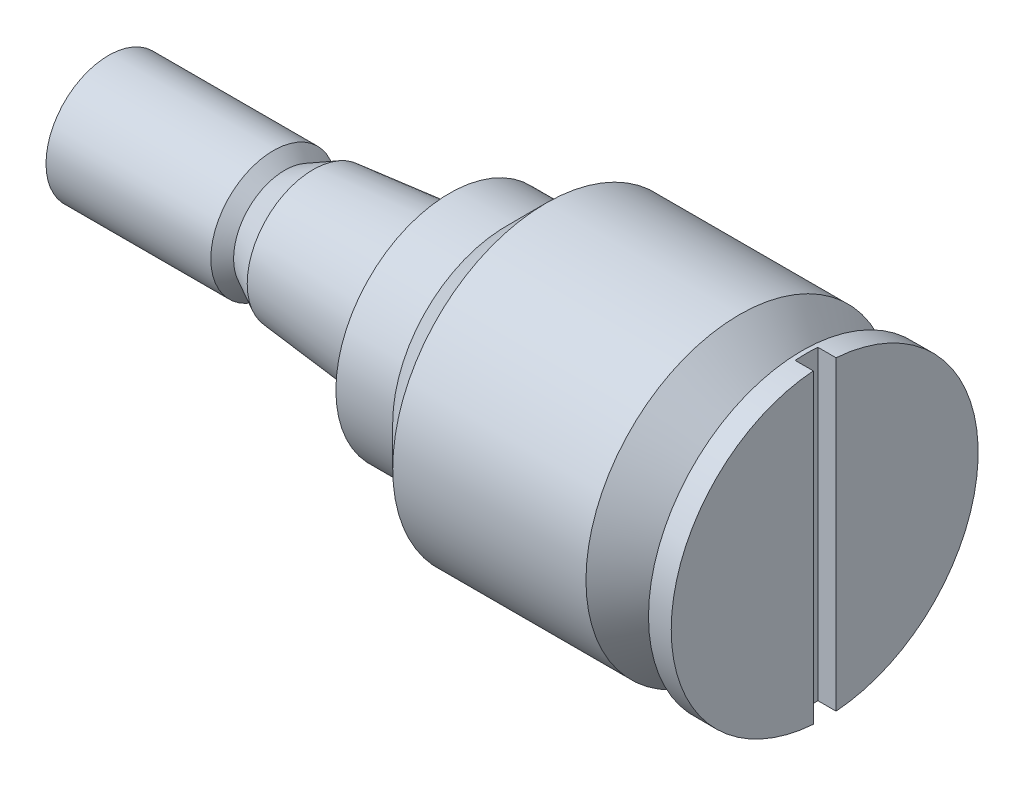
SolidWorks part; units mm, degrees
ref_plane "Спереди" through (0, 0, 0) normal (0, 0, 1) x (1, 0, 0)
ref_plane "Сверху" through (0, 0, 0) normal (0, 1, 0) x (1, 0, 0)
ref_plane "Справа" through (0, 0, 0) normal (1, 0, 0) x (0, 0, -1)
sketch "Эскиз1" plane through (0, 0, 0) normal (0, 0, 1) x (1, 0, 0)
  line L0 (-31.5, 0) -> (31.5, 0)
  line L1 (31.5, 0) -> (31.5, 13.5)
  line L2 (31.5, 13.5) -> (29.5, 13.5)
  line L3 (29.5, 13.5) -> (29.5, 10)
  line L4 (29.5, 10) -> (27.5, 10)
  line L5 (27.5, 10) -> (24, 13.5)
  line L6 (24, 13.5) -> (7, 13.5)
  line L7 (7, 13.5) -> (3.5, 10)
  line L8 (-1.5, 7) -> (-1.5, 10)
  line L9 (-1.5, 7) -> (-13.5, 5.8)
  line L10 (-1.5, 10) -> (3.5, 10)
  line L11 (-31.5, 5.5) -> (-31.5, 0)
  line L12 (-320.1149, 10.8197) -> (-320.1149, 0.8197) construction
  line L13 (-320.1149, 0.8197) -> (-420.1149, 0.8197) construction
  line L14 (-420.1149, 0.8197) -> (-320.1149, 10.8197) construction
  line L15 (-31.5, 5.5) -> (-17, 5.5)
  line L16 (-17, 5.5) -> (-16, 4.5)
  line L17 (-16, 4.5) -> (-13.5, 5.8)
  line L18 (-261.9182, 0) -> (229.0654, 0) construction
  point P21 (0, 0)
  dimension "D1" = 100
  dimension "D2" = 10
  dimension "D3" = 1
  dimension "d_1" = 11
  dimension "l_2" = 2.5
  dimension "l_ps" = 45
  dimension "d_r" = 20
  dimension "d_p" = 14
  dimension "l_1" = 2
  dimension "l_v" = 28
  dimension "d_2" = 20
  dimension "l_p" = 63
  dimension "s_" = 5
  dimension "D4" = 1
  dimension "d_g" = 27
  dimension "D5" = 2
  dimension "d_v" = 27
  dimension "D6" = 45
revolve "Повернуть1" add sketch "Эскиз1" angle 360 about L18
sketch "Эскиз2" plane through (0, 0, 0) normal (0, 1, 0) x (1, 0, 0)
  line L0 (31.5, -13.5) -> (31.5, 13.5) construction
  line L1 (31.5, 1) -> (29.9, 1)
  line L2 (31.5, 1) -> (31.5, -1)
  line L3 (31.5, -1) -> (29.9, -1)
  line L4 (29.9, 1) -> (29.9, -1)
  line L5 (31.5, 1) -> (29.9, -1) construction
  line L6 (31.5, -1) -> (29.9, 1) construction
  point P0 (30.7, 0)
  dimension "D1" = 2
  dimension "D2" = 1.6
extrude "Вырез-Вытянуть1" cut sketch "Эскиз2" against normal through all both and the other way through all
equation "\"d_1\" = 11"
equation "\"d_1@Эскиз1\"=\"d_1\""
equation "\"l_2\" = 2.5"
equation "\"l_2@Эскиз1\"=\"l_2\""
equation "\"l_ps\" = 45"
equation "\"l_ps@Эскиз1\"=\"l_ps\""
equation "\"d_p\" = 14"
equation "\"d_r\" = 20"
equation "\"d_r@Эскиз1\"=\"d_r\""
equation "\"d_p@Эскиз1\"=\"d_p\""
equation "\"l_1\" = 2"
equation "\"l_1@Эскиз1\"=\"l_1\""
equation "\"l_v\" = 28"
equation "\"l_v@Эскиз1\"=\"l_v\""
equation "\"d_2\" = 20"
equation "\"d_2@Эскиз1\"=\"d_2\""
equation "\"l_p\" = 63"
equation "\"l_p@Эскиз1\"=\"l_p\""
equation "\"s_\"= 5"
equation "\"s_@Эскиз1\"=\"s_\""
equation "\"d_v\"=27"
equation "\"d_g@Эскиз1\"=\"d_v\""
equation "\"d_v@Эскиз1\"=\"d_v\""
